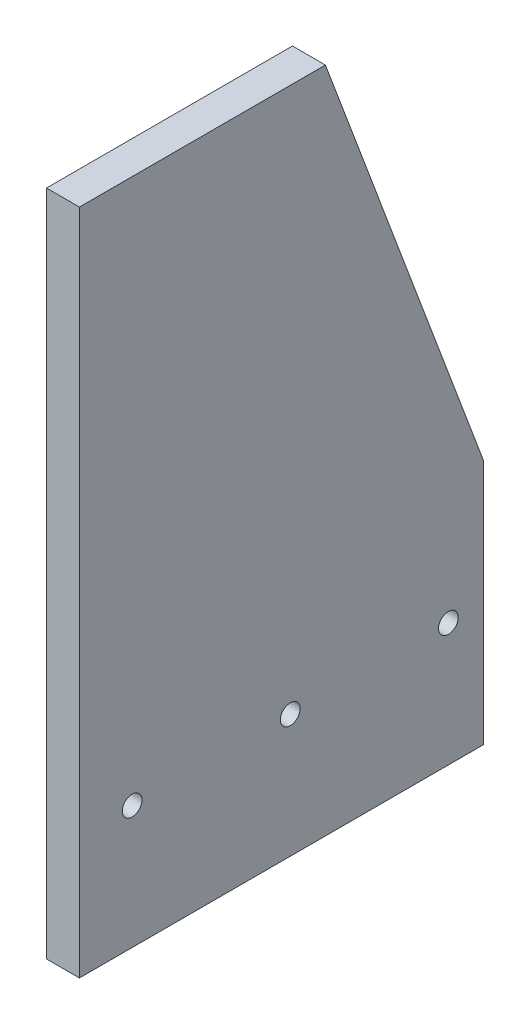
SolidWorks part; units mm, degrees
material "Pine"
ref_plane "Front Plane" through (0, 0, 0) normal (0, 0, 1) x (1, 0, 0)
ref_plane "Top Plane" through (0, 0, 0) normal (0, 1, 0) x (1, 0, 0)
ref_plane "Right Plane" through (0, 0, 0) normal (1, 0, 0) x (0, 0, -1)
sketch "Sketch1" plane through (0, 0, 0) normal (1, 0, 0) x (0, 0, -1)
  line L0 (0, 0) -> (0, 241.3)
  line L1 (0, 241.3) -> (88.9, 241.3)
  line L2 (88.9, 241.3) -> (146.05, 88.9)
  line L3 (146.05, 88.9) -> (146.05, 0)
  line L4 (146.05, 0) -> (0, 0)
  circle A0 centre (19.05, 44.45) radius 3.5719
  circle A1 centre (76.2, 44.45) radius 3.5719
  circle A2 centre (133.35, 44.45) radius 3.5719
  dimension "D5" = 7.1437
  dimension "D1" = 146.05
  dimension "D2" = 88.9
  dimension "D3" = 88.9
  dimension "D4" = 241.3
  dimension "D6" = 44.45
  dimension "D7" = 19.05
  dimension "D8" = 57.15
  dimension "D9" = 57.15
extrude "Boss-Extrude1" add sketch "Sketch1" along normal blind 11.9062
